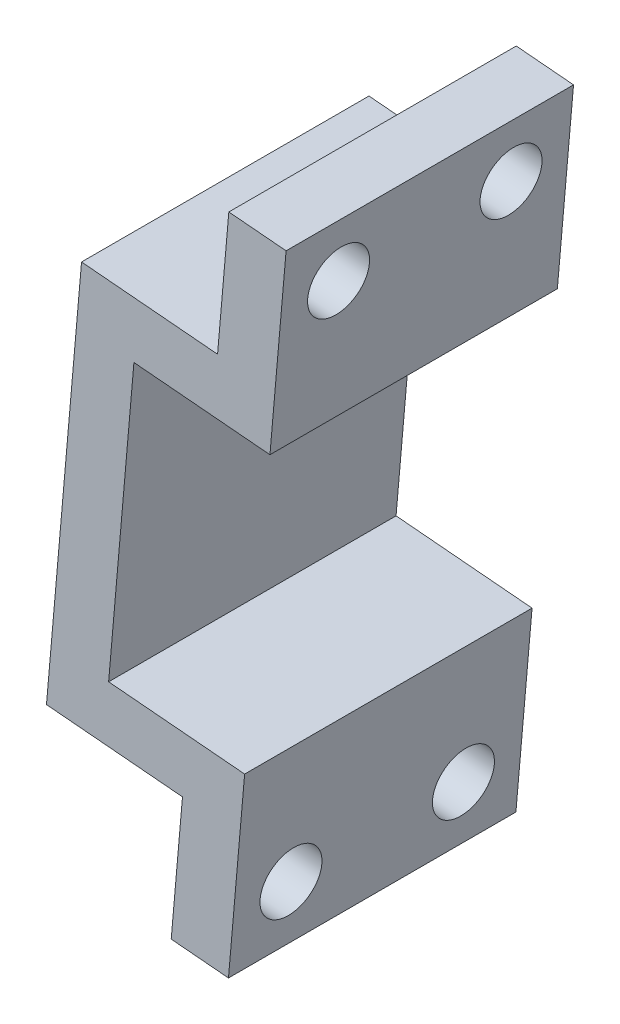
SolidWorks part; units mm, degrees
ref_plane "前视基准面" through (0, 0, 0) normal (0, 0, 1) x (1, 0, 0)
ref_plane "上视基准面" through (0, 0, 0) normal (0, 1, 0) x (1, 0, 0)
ref_plane "右视基准面" through (0, 0, 0) normal (1, 0, 0) x (0, 0, -1)
sketch "Sketch1" plane through (0, 0, 0) normal (0, 0, 1) x (1, 0, 0)
  line L0 (-80.6536, 18.9611) -> (-76.6688, 18.6124)
  line L1 (-76.6688, 18.6124) -> (-77.7931, 5.7615)
  line L2 (-77.7931, 5.7615) -> (-87.257, 6.5895)
  line L3 (-87.257, 6.5895) -> (-89.0175, -13.5336)
  line L4 (-89.0175, -13.5336) -> (-79.5537, -14.3616)
  line L5 (-79.5537, -14.3616) -> (-80.678, -27.2125)
  line L6 (-80.678, -27.2125) -> (-84.6627, -26.8639)
  line L7 (-84.6627, -26.8639) -> (-83.8783, -17.8981)
  line L8 (-83.8783, -17.8981) -> (-93.3422, -17.0702)
  line L9 (-93.3422, -17.0702) -> (-90.9018, 10.8233)
  line L10 (-90.9018, 10.8233) -> (-81.438, 9.9953)
  line L11 (-81.438, 9.9953) -> (-80.6536, 18.9611)
  dimension "D1" = 4
  dimension "D2" = 3.9
  dimension "D3" = 3.9
  dimension "D4" = 4
  dimension "D5" = 9.5
extrude "Boss-Extrude1" add sketch "Sketch1" against normal blind 20
sketch "Sketch2" plane through (-81.6872, 7.1467, 0) normal (-0.9962, 0.0872, 0) x (0, 0, 1)
  circle A4 centre (-4, -30.1405) radius 2.15
  circle A5 centre (-16, -30.1405) radius 2.15
  circle A6 centre (-4, 7.8595) radius 2.15
  circle A7 centre (-16, 7.8595) radius 2.15
extrude "Cut-Extrude1" cut sketch "Sketch2" against normal blind 5
